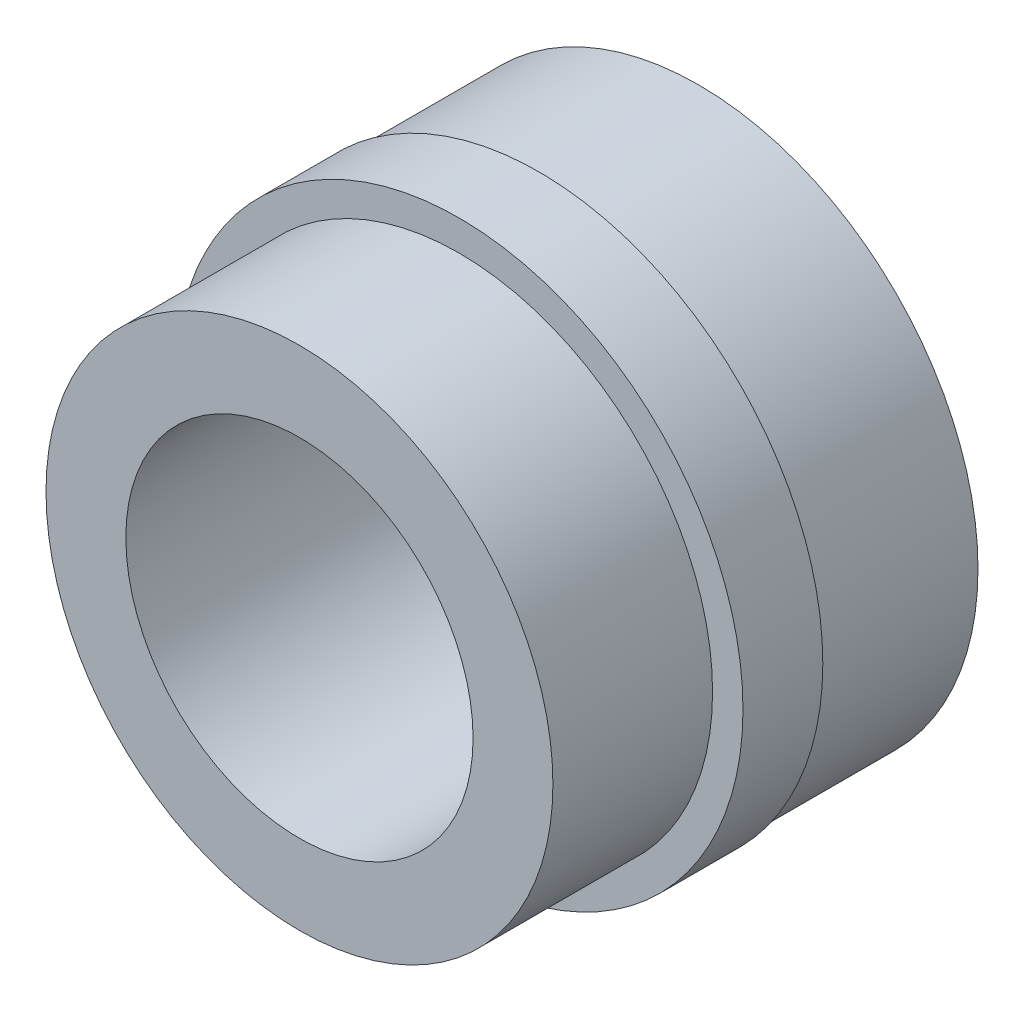
SolidWorks part; units mm, degrees
material "Plain Carbon Steel"
ref_plane "Front Plane" through (0, 0, 0) normal (0, 0, 1) x (1, 0, 0)
ref_plane "Top Plane" through (0, 0, 0) normal (0, 1, 0) x (1, 0, 0)
ref_plane "Right Plane" through (0, 0, 0) normal (1, 0, 0) x (0, 0, -1)
sketch "Sketch1" plane through (0, 0, 0) normal (1, 0, 0) x (0, 0, -1)
  line L0 (-52.0138, 0) -> (52.0138, 0) construction
  line L1 (-6, 6.525) -> (-6, 9.525)
  line L2 (-6, 9.525) -> (0, 9.525)
  line L3 (0, 9.525) -> (0, 10.668)
  line L4 (0, 10.668) -> (3, 10.668)
  line L5 (3, 10.668) -> (3, 10.5)
  line L6 (3, 10.5) -> (9, 10.5)
  line L7 (9, 10.5) -> (9, 6.525)
  line L8 (-6, 6.525) -> (9, 6.525)
  dimension "D1" = 19.05
  dimension "D2" = 6
  dimension "D3" = 6
  dimension "D4" = 3
  dimension "D5" = 21
  dimension "D6" = 21.336
  dimension "D7" = 3
revolve "Revolve1" add sketch "Sketch1" angle 360 about L0
